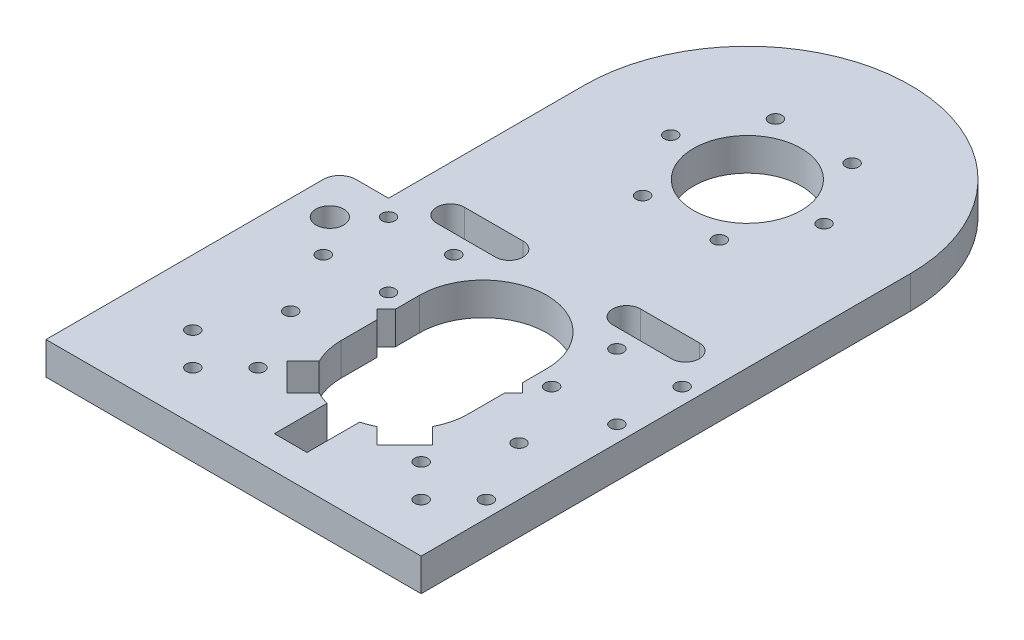
SolidWorks part; units mm, degrees
material "Acrylic (Medium-high impact)"
ref_plane "Front Plane" through (0, 0, 0) normal (0, 0, 1) x (1, 0, 0)
ref_plane "Top Plane" through (0, 0, 0) normal (0, 1, 0) x (1, 0, 0)
ref_plane "Right Plane" through (0, 0, 0) normal (1, 0, 0) x (0, 0, -1)
sketch "Sketch1" plane through (0, 0, 0) normal (0, 1, 0) x (1, 0, 0)
  line L0 (-2.3264, 11.6598) -> (-2.3264, -10.986) construction
  line L1 (-25.8407, 8.1193) -> (-12.3264, 8.1193) construction
  line L2 (-2.3264, 11.6598) -> (-2.3264, -10.986)
  line L3 (-52.3264, -141.8807) -> (47.6736, -141.8807)
  line L4 (47.6736, -141.8807) -> (47.6736, 8.1193)
  line L5 (-2.3264, 8.1193) -> (25.1292, 8.1193) construction
  line L6 (-52.3264, -141.8807) -> (-52.3264, 8.1193)
  arc A0 (47.6736, 8.1193) -> (-52.3264, 8.1193) centre (-2.3264, 8.1193) ccw
  circle A1 centre (-2.3264, 8.1193) radius 16.5
  circle A2 centre (-2.3264, 8.1193) radius 23.5 construction
  circle A3 centre (21.1736, 8.1193) radius 2
  circle A4 centre (9.4236, -12.2323) radius 2
  circle A5 centre (-14.0764, -12.2323) radius 2
  circle A6 centre (-25.8264, 8.1193) radius 2
  circle A7 centre (-14.0764, 28.4709) radius 2
  circle A8 centre (9.4236, 28.4709) radius 2
  circle A9 centre (-47.3264, -116.8807) radius 2
  circle A10 centre (42.6736, -116.8807) radius 2
  circle A11 centre (-37.3264, -126.8807) radius 2
  circle A12 centre (-37.3264, -96.8807) radius 2
  circle A13 centre (-47.3264, -76.8807) radius 2
  circle A14 centre (42.6736, -76.8807) radius 2
  circle A15 centre (-47.3264, -56.8807) radius 2
  circle A16 centre (42.6736, -56.8807) radius 2
  circle A17 centre (-27.3264, -116.8807) radius 2
  circle A18 centre (22.6736, -116.8807) radius 2
  circle A19 centre (-27.3264, -56.8807) radius 2
  circle A20 centre (-27.3264, -76.8807) radius 2
  circle A21 centre (22.6736, -56.8807) radius 2
  circle A22 centre (22.6736, -76.8807) radius 2
  circle A23 centre (32.6736, -96.8807) radius 2
  circle A24 centre (32.6736, -126.8807) radius 2
  point P26 (-2.3264, 8.1193)
  dimension "D1" = 100
  dimension "D3" = 33
  dimension "D4" = 47
  dimension "D5" = 4
  dimension "D7" = 4
  dimension "D8" = 4
  dimension "D9" = 4
  dimension "D10" = 4
  dimension "D11" = 4
  dimension "D12" = 4
  dimension "D13" = 4
  dimension "D14" = 4
  dimension "D20" = 4
  dimension "D21" = 4
  dimension "D22" = 4
  dimension "D23" = 4
  dimension "D24" = 4
  dimension "D25" = 4
  dimension "D28" = 4
  dimension "D54" = 4
  dimension "D2" = 150
  dimension "D6" = 6
  dimension "D15" = 25
  dimension "D16" = 5
  dimension "D17" = 25
  dimension "D18" = 5
  dimension "D19" = 15
  dimension "D26" = 25
  dimension "D27" = 20
  dimension "D29" = 20
  dimension "D30" = 25
  dimension "D31" = 15
  dimension "D32" = 45
  dimension "D33" = 15
  dimension "D34" = 15
  dimension "D35" = 15
  dimension "D36" = 15
  dimension "D37" = 45
  dimension "D38" = 5
  dimension "D39" = 5
  dimension "D40" = 5
  dimension "D41" = 5
  dimension "D42" = 85
  dimension "D43" = 85
  dimension "D44" = 20
  dimension "D45" = 20
  dimension "D46" = 20
  dimension "D47" = 20
  dimension "D48" = 85
  dimension "D49" = 20
  dimension "D50" = 20
  dimension "D51" = 20
  dimension "D52" = 20
  dimension "D53" = 85
extrude "Boss-Extrude3" add sketch "Sketch1" along normal blind 10
sketch "Sketch2" plane through (0, 10, 0) normal (0, 1, 0) x (1, 0, 0)
  line L0 (-52.3264, -141.8807) -> (-52.3264, 8.1193) construction
  line L2 (-52.3264, -141.8807) -> (47.6736, -141.8807) construction
  circle A0 centre (-2.3264, -96.8807) radius 19.5
  point P6 (-52.3264, -66.8807)
  dimension "D1" = 39
  dimension "D2" = 50
  dimension "D3" = 45
extrude "Cut-Extrude1" cut sketch "Sketch2" against normal blind 10
sketch "Sketch3" plane through (0, 10, 0) normal (0, 1, 0) x (1, 0, 0)
  line L0 (-7.3264, -131.8807) -> (-7.3264, -115.7288)
  line L1 (-52.3264, -141.8807) -> (47.6736, -141.8807) construction
  line L2 (2.6736, -131.8807) -> (2.6736, -115.7288)
  line L3 (-52.3264, -141.8807) -> (-52.3264, 8.1193) construction
  line L4 (-7.3264, -131.8807) -> (2.6736, -131.8807)
  circle A0 centre (-2.3264, -96.8807) radius 19.5 construction
  arc A1 (-7.3264, -115.7288) -> (2.6736, -115.7288) centre (-2.3264, -96.8807) ccw
  dimension "D1" = 10
  dimension "D2" = 45
  dimension "D3" = 10
extrude "Cut-Extrude2" cut sketch "Sketch3" against normal blind 10
sketch "Sketch4" plane through (0, 10, 0) normal (0, 1, 0) x (1, 0, 0)
  line L0 (-2.3264, -96.8807) -> (-2.3264, -84.8807) construction
  line L1 (6.5506, -79.5184) -> (11.4622, -74.6068)
  line L2 (11.4622, -74.6068) -> (19.9475, -83.0921)
  line L3 (15.0359, -88.0037) -> (19.9475, -83.0921)
  line L12 (15.0359, -105.7577) -> (19.9475, -110.6693)
  line L13 (19.9475, -110.6693) -> (11.4622, -119.1545)
  line L14 (6.5506, -114.243) -> (11.4622, -119.1545)
  line L18 (-11.2034, -114.243) -> (-16.115, -119.1545)
  line L19 (-16.115, -119.1545) -> (-24.6003, -110.6693)
  line L20 (-19.6887, -105.7577) -> (-24.6003, -110.6693)
  line L24 (-19.6887, -88.0037) -> (-24.6003, -83.0921)
  line L25 (-24.6003, -83.0921) -> (-16.115, -74.6068)
  line L26 (-11.2034, -79.5184) -> (-16.115, -74.6068)
  arc A0 (2.6736, -115.7288) -> (-7.3264, -115.7288) centre (-2.3264, -96.8807) ccw construction
  arc A1 (2.6736, -115.7288) -> (-1.3168, -77.4068) centre (-2.3264, -96.8807) ccw
  arc A2 (2.6736, -115.7288) -> (-7.3264, -115.7288) centre (-2.3264, -96.8807) ccw
  point P2 (-2.3264, -77.3807)
  point P42 (-2.3264, -96.8807)
  arc M29 (-7.3264, -115.7288) -> (2.6736, -115.7288) centre (-2.3264, -96.8807) cw
extrude "Cut-Extrude3" cut sketch "Sketch4" against normal blind 10 contours L26 L25 L24 M29 | L3 L2 L1 M29 | L14 L13 L12 M29 | L20 L19 L18 M29
sketch "Sketch8" plane through (0, 10, 0) normal (0, 1, 0) x (1, 0, 0)
  line L1 (-21.8264, -96.8807) -> (17.1736, -96.8807)
  line L2 (-21.8264, -96.8807) -> (-21.8264, -72.8807)
  line L4 (17.1736, -96.8807) -> (17.1736, -72.8807)
  arc A0 (-19.6887, -88.0037) -> (-19.6887, -105.7577) centre (-2.3264, -96.8807) ccw construction
  arc A1 (17.1736, -72.8807) -> (-21.8264, -72.8807) centre (-2.3264, -72.8807) ccw
  dimension "D3" = 39
  dimension "D1" = 39
  dimension "D2" = 24
extrude "Cut-Extrude6" cut sketch "Sketch8" against normal blind 10
sketch "Sketch9" plane through (-52.3264, 0, 0) normal (-1, 0, 0) x (0, 0, 1)
  line L0 (141.8807, 0) -> (-8.1193, 0) construction
  line L1 (141.8807, 10) -> (51.8807, 10)
  line L2 (141.8807, 10) -> (141.8807, 0)
  line L3 (141.8807, 0) -> (51.8807, 0)
  line L4 (51.8807, 10) -> (51.8807, 0)
  dimension "D1" = 90
extrude "Boss-Extrude4" add sketch "Sketch9" along normal blind 15
fillet "Fillet1" radius 5 1 edges at (-67.3264, 5, 51.8807)
sketch "Sketch10" plane through (0, 10, 0) normal (0, 1, 0) x (1, 0, 0)
  line L0 (-52.3264, -51.8807) -> (-52.3264, 8.1193) construction
  line L1 (-62.3264, -51.8807) -> (-52.3264, -51.8807) construction
  circle A0 centre (-56.3264, -65.8807) radius 4.25
  dimension "D1" = 8.5
  dimension "D2" = 4
  dimension "D3" = 14
extrude "Cut-Extrude7" cut sketch "Sketch10" against normal blind 10
sketch "Sketch11" plane through (0, 10, 0) normal (0, 1, 0) x (1, 0, 0)
  line L0 (-67.3264, -141.8807) -> (47.6736, -141.8807) construction
  line L1 (47.6736, -141.8807) -> (47.6736, 8.1193) construction
  line L2 (15.6736, -42.6307) -> (33.6736, -42.6307)
  line L3 (15.6736, -51.1307) -> (33.6736, -51.1307)
  line L4 (-52.3264, -51.8807) -> (-52.3264, 8.1193) construction
  line L5 (-38.3264, -42.6307) -> (-20.3264, -42.6307)
  line L6 (-38.3264, -51.1307) -> (-20.3264, -51.1307)
  arc A0 (15.6736, -42.6307) -> (15.6736, -51.1307) centre (15.6736, -46.8807) ccw
  arc A1 (-20.3264, -51.1307) -> (-20.3264, -42.6307) centre (-20.3264, -46.8807) ccw
  arc A2 (33.6736, -51.1307) -> (33.6736, -42.6307) centre (33.6736, -46.8807) ccw
  arc A3 (-38.3264, -42.6307) -> (-38.3264, -51.1307) centre (-38.3264, -46.8807) ccw
  dimension "D1" = 8.5
  dimension "D2" = 8.5
  dimension "D5" = 8.5
  dimension "D10" = 8.5
  dimension "D3" = 95
  dimension "D4" = 32
  dimension "D6" = 14
  dimension "D7" = 95
  dimension "D8" = 95
  dimension "D9" = 32
  dimension "D11" = 14
  dimension "D12" = 95
extrude "Cut-Extrude8" cut sketch "Sketch11" against normal blind 10 contours A1 L5 A3 L6 | A2 L2 A0 L3
